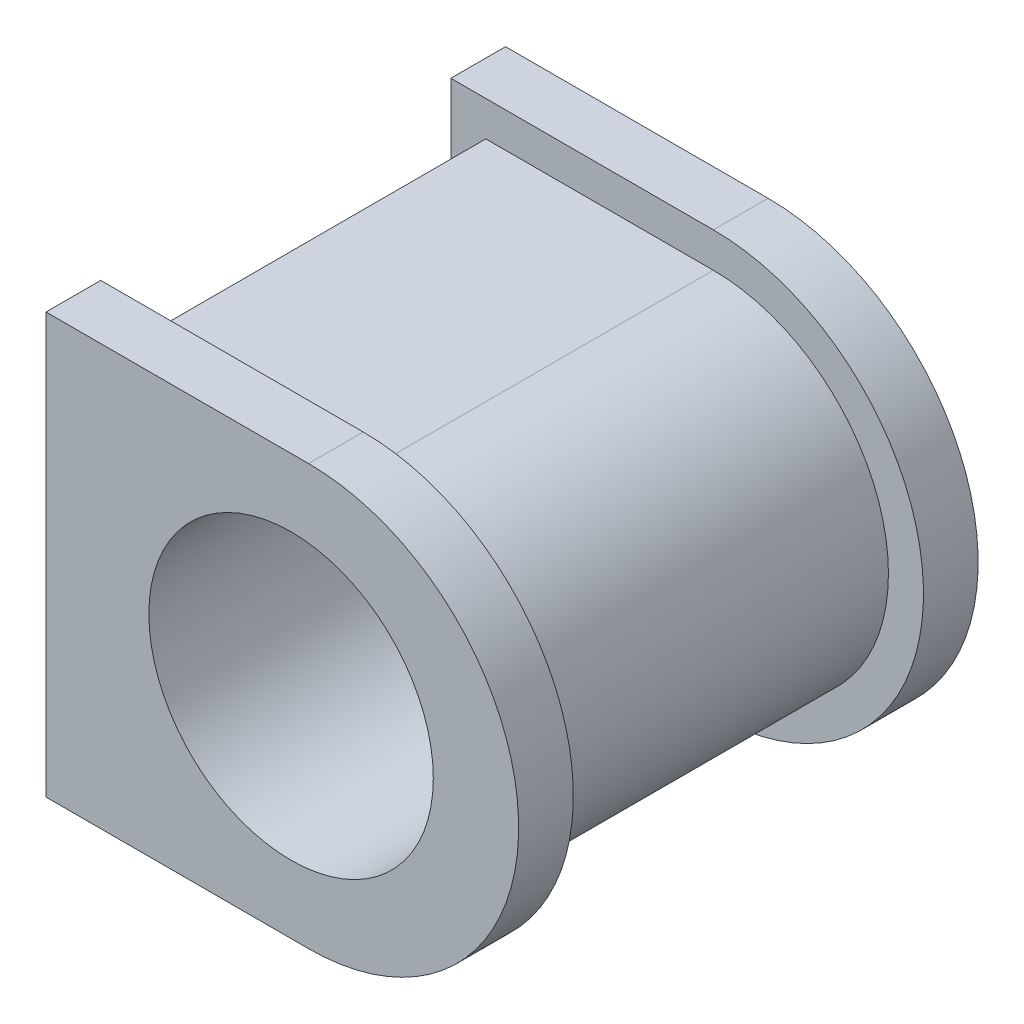
SolidWorks part; units mm, degrees
ref_plane "Front Plane" through (0, 0, 0) normal (0, 0, 1) x (1, 0, 0)
ref_plane "Top Plane" through (0, 0, 0) normal (0, 1, 0) x (1, 0, 0)
ref_plane "Right Plane" through (0, 0, 0) normal (1, 0, 0) x (0, 0, -1)
sketch "Sketch1" plane through (0, 0, 0) normal (0, 0, 1) x (1, 0, 0)
  line L1 (-225.7926, 137.875) -> (-173.7926, 137.875)
  line L2 (-225.7926, 137.875) -> (-225.7926, 57.875)
  line L3 (-225.7926, 57.875) -> (-173.7926, 57.875)
  circle A1 centre (-177.7926, 97.875) radius 32.5
  arc A2 (-173.7926, 57.875) -> (-173.7926, 137.875) centre (-173.7926, 97.875) ccw
  point P0 (-201.7926, 97.875)
extrude "Boss-Extrude1" add sketch "Sketch1" along normal blind 80
sketch "Sketch2" plane through (0, 0, 80) normal (0, 0, 1) x (1, 0, 0)
  line L0 (-225.7926, 137.875) -> (-225.7926, 57.875)
  line L3 (-173.7926, 145.875) -> (-233.7926, 145.875)
  line L4 (-173.7926, 49.875) -> (-233.7926, 49.875)
  line L5 (-233.7926, 145.875) -> (-233.7926, 49.875)
  arc A0 (-173.7926, 49.875) -> (-173.7926, 145.875) centre (-173.7926, 97.875) ccw
  line M3 (-225.7926, 137.875) -> (-225.7926, 57.875)
  line M4 (-225.7926, 57.875) -> (-173.7926, 57.875)
  arc M5 (-173.7926, 57.875) -> (-173.7926, 137.875) centre (-173.7926, 97.875) ccw
  line M6 (-173.7926, 137.875) -> (-225.7926, 137.875)
  circle M7 centre (-177.7926, 97.875) radius 32.5
extrude "Boss-Extrude2" add sketch "Sketch2" along normal blind 12.5 contours L4 A0 L3 L5 M3 M6 M5 M4 | M6 M3 M4 M5 M7
sketch "Sketch6" plane through (0, 0, 0) normal (0, 0, -1) x (-1, 0, 0)
  line L0 (233.7926, 145.875) -> (173.7926, 145.875)
  line L1 (233.7926, 145.875) -> (233.7926, 49.875)
  line L2 (233.7926, 49.875) -> (173.7926, 49.875)
  arc A0 (173.7926, 145.875) -> (173.7926, 49.875) centre (173.7926, 97.875) ccw
  circle A1 centre (177.7926, 97.875) radius 32.5
extrude "Boss-Extrude4" add sketch "Sketch6" along normal blind 12.5
